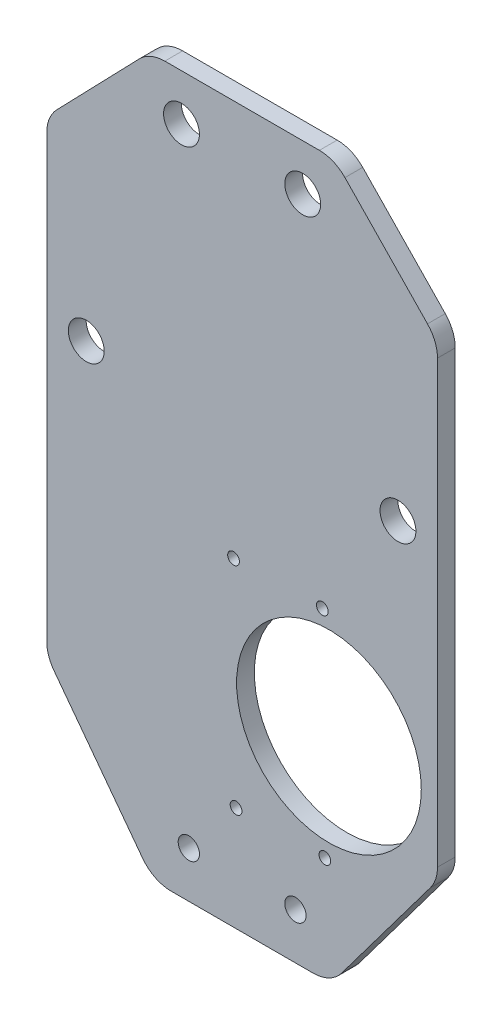
SolidWorks part; units mm, degrees
ref_plane "前视基准面" through (0, 0, 0) normal (0, 0, 1) x (1, 0, 0)
ref_plane "上视基准面" through (0, 0, 0) normal (0, 1, 0) x (1, 0, 0)
ref_plane "右视基准面" through (0, 0, 0) normal (1, 0, 0) x (0, 0, -1)
sketch "草图1" plane through (0, 0, 0) normal (0, 0, 1) x (1, 0, 0)
  line L0 (-25, 0) -> (25, 0)
  line L1 (0, 0) -> (0, 201.5) construction
  line L2 (-26, 201.5) -> (26, 201.5)
  line L3 (25, 0) -> (55, 40)
  line L4 (55, 40) -> (55, 171.5)
  line L5 (55, 171.5) -> (26, 201.5)
  line L6 (-25, 0) -> (-55, 40)
  line L7 (-55, 40) -> (-55, 171.5)
  line L8 (-55, 171.5) -> (-26, 201.5)
  line L10 (-17.0625, 188.4995) -> (17.0625, 188.4995) construction
  line L11 (-43.875, 122.2173) -> (43.875, 122.2173) construction
  line L12 (-28.4296, 127.2673) -> (28.4296, 127.2673) construction
  line L13 (-28.4296, 117.1673) -> (28.4296, 117.1673) construction
  line L14 (-43.875, 105.9673) -> (-43.875, 57.2173) construction
  circle A0 centre (24.439, 60) radius 26
  circle A1 centre (15, 13) radius 3
  circle A2 centre (-15, 13) radius 3
  circle A3 centre (-17.0625, 188.4995) radius 5.05
  circle A4 centre (17.0625, 188.4995) radius 5.05
  circle A5 centre (-43.875, 122.2173) radius 5.05
  circle A6 centre (43.875, 122.2173) radius 5.05
  arc A7 (-28.4296, 127.2673) -> (-40.8657, 138.1862) centre (-43.875, 122.2173) ccw construction
  arc A8 (32.8919, 99.7359) -> (-16.1331, 57.9259) centre (24.439, 60) ccw construction
  arc A9 (28.4296, 117.1673) -> (35.9887, 108.0092) centre (43.875, 122.2173) ccw construction
  arc A10 (40.8657, 138.1862) -> (-40.8657, 138.1862) centre (0, 122.2173) ccw construction
  arc A11 (-43.875, 105.9673) -> (-28.4296, 117.1673) centre (-43.875, 122.2173) ccw construction
  arc A12 (-43.875, 57.2173) -> (-16.1331, 57.9259) centre (-29.995, 57.2173) ccw construction
  arc A13 (32.8919, 99.7359) -> (35.9887, 108.0092) centre (33.8212, 104.1043) ccw construction
  arc A14 (40.8657, 138.1862) -> (28.4296, 127.2673) centre (43.875, 122.2173) ccw construction
  point P7 (0, 201.5)
  point P17 (55, 40)
  point P24 (0, 188.4995)
  point P27 (0, 122.2173)
  dimension "D7" = 43.875
  dimension "D13" = 52
  dimension "D14" = 60
  dimension "D19" = 16.25
  dimension "D20" = 16.25
  dimension "D21" = 40.625
  dimension "D23" = 33.8212
  dimension "D22" = 65
  dimension "D24" = 10.1
  dimension "D12" = 6
  dimension "D15" = 24.439
  dimension "D17" = 10.1
  dimension "D18" = 87.75
  dimension "D1" = 201.5
  dimension "D2" = 52
  dimension "D3" = 110
  dimension "D4" = 34.125
  dimension "D5" = 13.0005
  dimension "D6" = 30
  dimension "D8" = 122.2173
  dimension "D9" = 13
  dimension "D10" = 30
  dimension "D11" = 50
  dimension "D16" = 40
extrude "凸台-拉伸1" add sketch "草图1" along normal blind 5
fillet "圆角1" radius 10 8 edges at (25, 0, 2.5) (55, 40, 2.5) (-25, 0, 2.5) (-55, 40, 2.5) (26, 201.5, 2.5) (-26, 201.5, 2.5) (-55, 171.5, 2.5) (55, 171.5, 2.5)
hole_wizard "M4 螺纹孔1" positions "草图2" profile "草图3" tap size "M4" standard "ISO"
sketch "草图2" plane through (0, 0, 0) normal (0, 0, -1) x (-1, 0, 0)
  point P0 (2.4131, 89.9379)
  point P3 (-22.5852, 90.2304)
  point P6 (1.7053, 29.442)
  point P9 (-23.293, 29.7345)
sketch "草图3" plane through (-2.4131, 89.9379, 0) normal (1, 0, 0) x (0, 1, 0)
  line L0 (0, 0) -> (0, 11.0914)
  line L1 (0, 11.0914) -> (1.65, 10.1)
  line L2 (1.65, 10.1) -> (1.65, 0)
  line L5 (1.65, 0) -> (0, 0)
  line L10 (0, 11.0914) -> (-1.65, 10.1) construction
  line L11 (0, -6.35) -> (0, 107.95) construction
  dimension "螺纹孔钻头直径" = 3.3
  dimension "螺纹孔钻头深度" = 10.1
  dimension "导头角度" = 118
cosmetic thread "孔螺蚊线1" parameters "D1"=5, "D2"=4
cosmetic thread "孔螺蚊线2" parameters "D1"=5, "D2"=4
cosmetic thread "孔螺蚊线3" parameters "D1"=5, "D2"=4
cosmetic thread "孔螺蚊线4" parameters "D1"=5, "D2"=4
